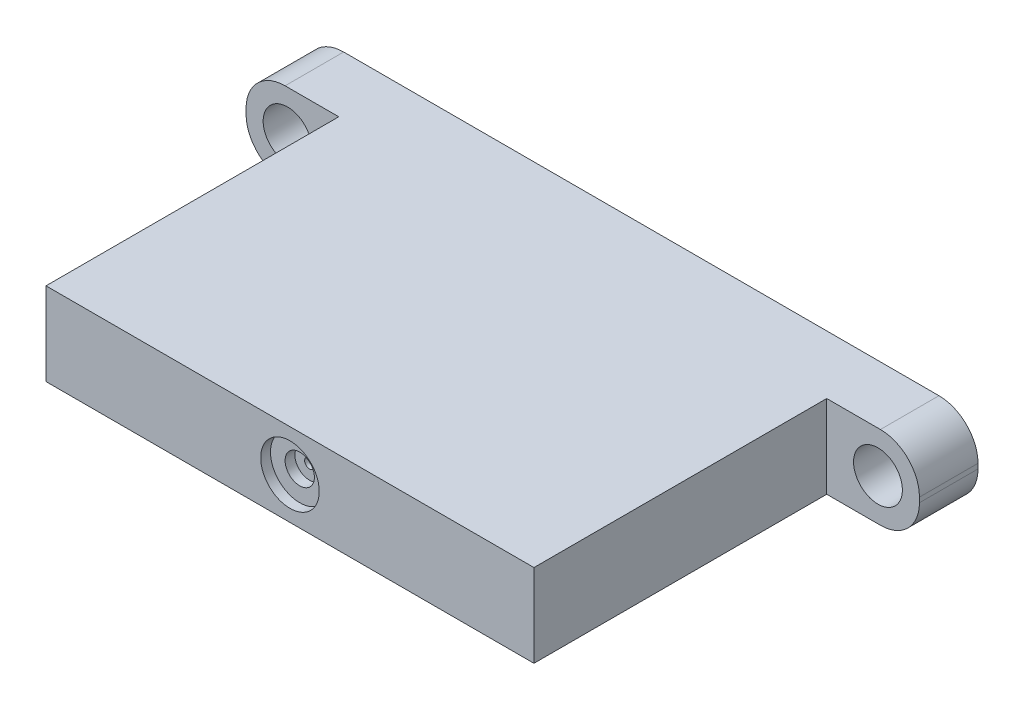
SolidWorks part; units mm, degrees
material "ABS"
ref_plane "Plano frontal" through (0, 0, 0) normal (0, 0, 1) x (1, 0, 0)
ref_plane "Plano superior" through (0, 0, 0) normal (0, 1, 0) x (1, 0, 0)
ref_plane "Plano direito" through (0, 0, 0) normal (1, 0, 0) x (0, 0, -1)
sketch "Esboço1" plane through (0, 0, 0) normal (0, 0, 1) x (1, 0, 0)
  line L0 (0, -38.996) -> (0, 38.262) construction
  line L1 (-44.2261, 0) -> (47.5293, 0) construction
  line L3 (34.5, -4.25) -> (-34.5, -4.25)
  line L4 (34.5, -4.25) -> (34.5, 4.25)
  line L5 (34.5, 4.25) -> (-34.5, 4.25)
  line L6 (-34.5, -4.25) -> (-34.5, 4.25)
  line L7 (34.5, -4.25) -> (-34.5, 4.25) construction
  line L8 (34.5, 4.25) -> (-34.5, -4.25) construction
  point P5 (0, 0)
  dimension "D1" = 69
  dimension "D2" = 8.5
extrude "Ressalto-extrusão1" add sketch "Esboço1" along normal blind 6
sketch "Esboço2" plane through (0, 0, 6) normal (0, 0, 1) x (1, 0, 0)
  line L0 (34.5, 4.25) -> (-34.5, 4.25) construction
  line L1 (25, -4.25) -> (-25, -4.25)
  line L2 (25, -4.25) -> (25, 4.25)
  line L3 (25, 4.25) -> (-25, 4.25)
  line L4 (-25, -4.25) -> (-25, 4.25)
  line L5 (25, -4.25) -> (-25, 4.25) construction
  line L6 (25, 4.25) -> (-25, -4.25) construction
  point P0 (0, 0)
  dimension "D1" = 50
extrude "Ressalto-extrusão2" add sketch "Esboço2" along normal blind 30
sketch "Esboço3" plane through (0, 0, 6) normal (0, 0, 1) x (1, 0, 0)
  line L0 (-39.5588, 0) -> (37.8755, 0) construction
  line L1 (0, -14.2384) -> (0, 17.3245) construction
  circle A0 centre (-30.25, 0) radius 2.5
  circle A1 centre (30.25, 0) radius 2.5
  dimension "D1" = 5
  dimension "D2" = 30.25
extrude "Corte-extrusão1" cut sketch "Esboço3" against normal through all
fillet "Filete1" radius 4 4 edges at (34.5, 4.25, 3) (34.5, -4.25, 3) (-34.5, -4.25, 3) (-34.5, 4.25, 3)
sketch "Esboço4" plane through (0, 0, 36) normal (0, 0, 1) x (1, 0, 0)
  line L0 (0, -11.3657) -> (0, 10.4699) construction
  line L1 (-39.8639, 0) -> (40.3118, 0) construction
  circle A0 centre (0, 0) radius 3
  dimension "D1" = 6
extrude "Corte-extrusão2" cut sketch "Esboço4" against normal blind 1
sketch "Esboço5" plane through (0, 0, 35) normal (0, 0, 1) x (1, 0, 0)
  line L0 (0, 8.1058) -> (0, -7.631) construction
  line L1 (-37.8923, 0) -> (36.3174, 0) construction
  circle A0 centre (0, 0) radius 1.5
  dimension "D1" = 3
extrude "Corte-extrusão3" cut sketch "Esboço5" against normal blind 1
sketch "Esboço6" plane through (0, 0, 34) normal (0, 0, 1) x (1, 0, 0)
  circle A0 centre (0, 0) radius 0.5
  dimension "D1" = 1
extrude "Corte-extrusão4" cut sketch "Esboço6" against normal blind 1
